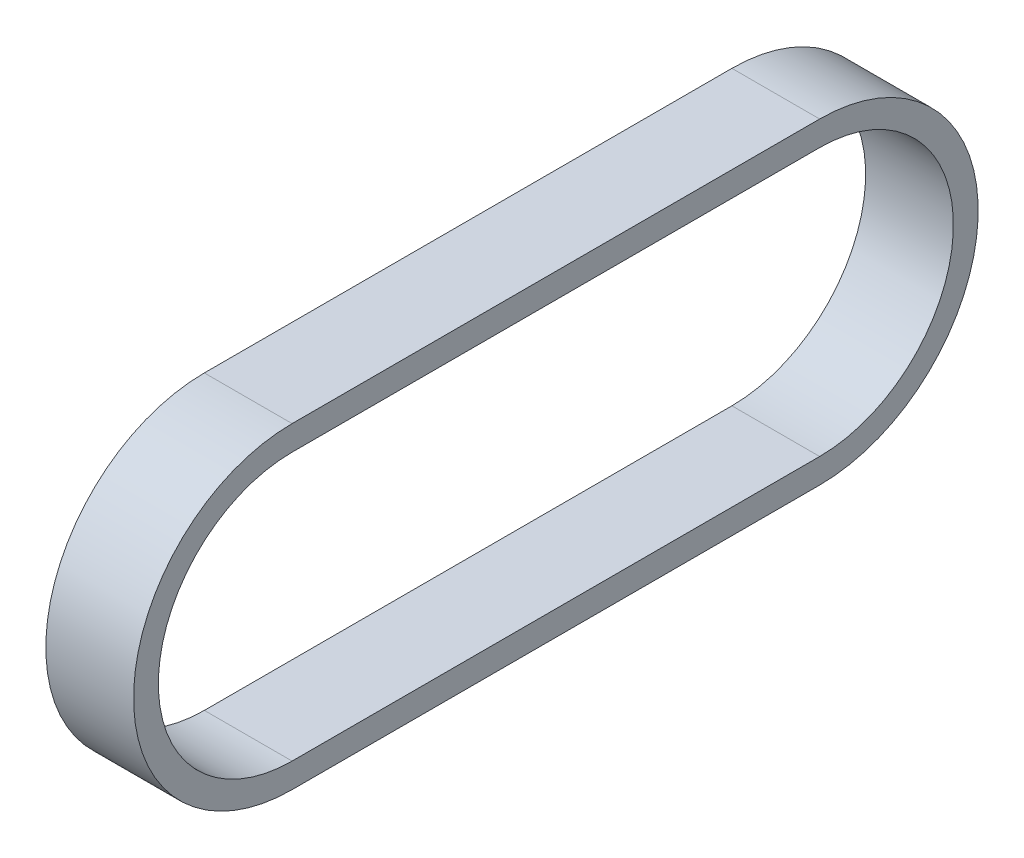
SolidWorks part; units mm, degrees
ref_plane "Front Plane" through (0, 0, 0) normal (0, 0, 1) x (1, 0, 0)
ref_plane "Top Plane" through (0, 0, 0) normal (0, 1, 0) x (1, 0, 0)
ref_plane "Right Plane" through (0, 0, 0) normal (1, 0, 0) x (0, 0, -1)
sketch "Sketch1" plane through (0, 0, 0) normal (1, 0, 0) x (0, 0, -1)
  line L0 (0, 0) -> (54.102, 0) construction
  line L1 (0, 13.716) -> (54.102, 13.716)
  line L2 (0, -13.716) -> (54.102, -13.716)
  arc A0 (0, 13.716) -> (0, -13.716) centre (0, 0) ccw
  arc A1 (54.102, -13.716) -> (54.102, 13.716) centre (54.102, 0) ccw
  dimension "D2" = 27.432
  dimension "D1" = 54.102
extrude "Extrude-Thin1" add sketch "Sketch1" along normal blind 9 thin thin type one direction wall 2.54
